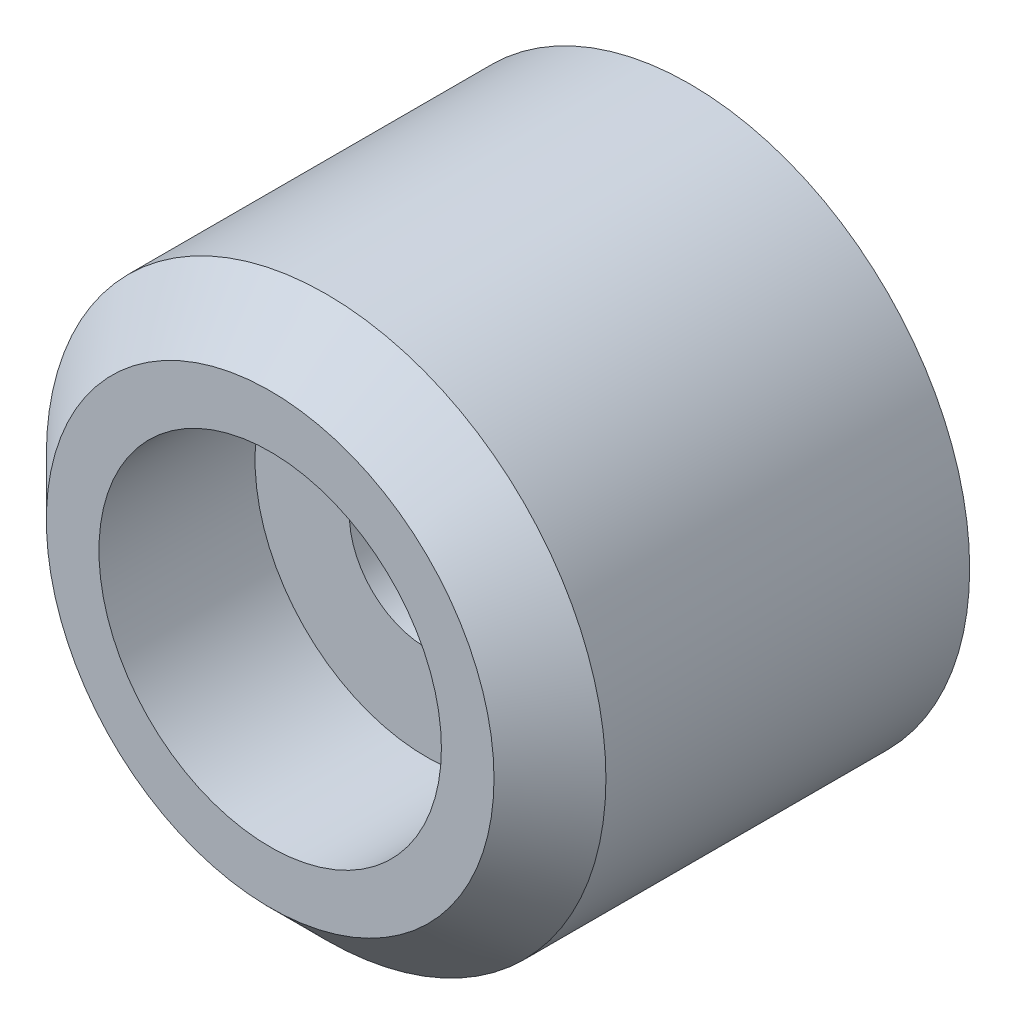
SolidWorks part; units mm, degrees
material "Natural rubber"
ref_plane "Front Plane" through (0, 0, 0) normal (0, 0, 1) x (1, 0, 0)
ref_plane "Top Plane" through (0, 0, 0) normal (0, 1, 0) x (1, 0, 0)
ref_plane "Right Plane" through (0, 0, 0) normal (1, 0, 0) x (0, 0, -1)
sketch "Sketch1" plane through (0, 0, 0) normal (0, 0, 1) x (1, 0, 0)
  circle A0 centre (0, 0) radius 10
  dimension "D1" = 20
extrude "Boss-Extrude1" add sketch "Sketch1" along normal blind 15
chamfer "Chamfer1" distance 2 angle 45 1 edges at (10, 0, 15)
ref_plane "Plane1" through (0, 0, 8) normal (0, 0, 1) x (1, 0, 0)
hole_wizard "CBORE for M5 Hex Head Bolt1" positions "Sketch3" profile "Sketch4" counterbore size "M5" standard "Ansi Metric" end condition through all
sketch "Sketch3" plane through (0, 0, 15) normal (0, 0, 1) x (1, 0, 0)
  point P0 (0, 0)
  dimension "D1" = 0
sketch "Sketch4" plane through (0, 0, 15) normal (1, 0, 0) x (0, -1, 0)
  line L0 (0, 0) -> (0, 15)
  line L1 (0, 15) -> (2.75, 15)
  line L3 (2.75, 15) -> (2.75, 5.58)
  line L4 (2.75, 5.58) -> (6.12, 5.58)
  line L5 (6.12, 5.58) -> (6.12, 0)
  line L7 (6.12, 0) -> (0, 0)
  line L11 (0, -6.35) -> (0, 107.95) construction
  dimension "Thru Hole Dia." = 5.5
  dimension "Thru Hole Depth" = 15
  dimension "C'Bore Dia." = 12.24
  dimension "C'Bore Depth" = 5.58
